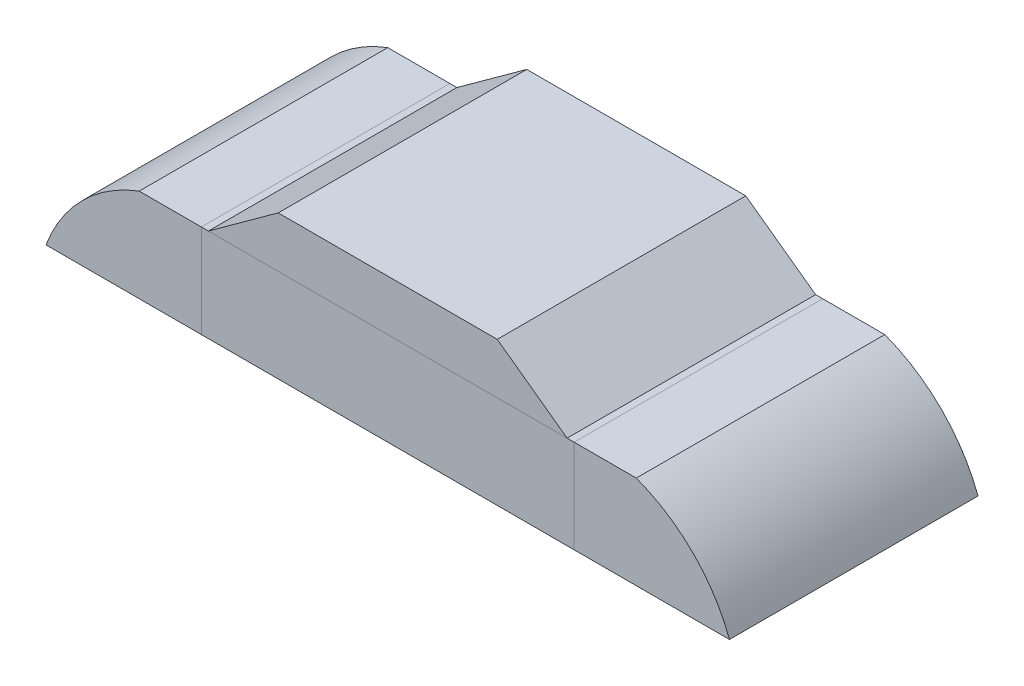
SolidWorks part; units mm, degrees
material "E-Glass Fiber"
ref_plane "Front Plane" through (0, 0, 0) normal (0, 0, 1) x (1, 0, 0)
ref_plane "Top Plane" through (0, 0, 0) normal (0, 1, 0) x (1, 0, 0)
ref_plane "Right Plane" through (0, 0, 0) normal (1, 0, 0) x (0, 0, -1)
sketch "Sketch1" plane through (0, 0, 0) normal (0, 1, 0) x (1, 0, 0)
  line L2 (-0.6, -0.4) -> (0.6, -0.4)
  line L3 (-0.6, -0.4) -> (-0.6, 0.4)
  line L4 (-0.6, 0.4) -> (0.6, 0.4)
  line L6 (0.6, -0.4) -> (0.6, 0.4)
  line L7 (-0.6, -0.4) -> (0.6, 0.4) construction
  line L8 (-0.6, 0.4) -> (0.6, -0.4) construction
  point P0 (0, 0)
  dimension "D1" = 1.2
  dimension "D2" = 0.8
extrude "Boss-Extrude1" add sketch "Sketch1" along normal blind 0.3
sketch "Sketch3" plane through (0, 0, 0) normal (0, 0, 1) x (1, 0, 0)
  line L0 (0, 0.8092) -> (0, -0.2421) construction
  line L2 (0, 0.4) -> (0.2, 0.4)
  line L3 (0, 0.4) -> (0, 0.3)
  line L4 (0, 0.3) -> (0.2, 0.3)
  line L5 (0.2, 0.4) -> (0.2, 0.3)
  line L8 (-0.6, 0.3) -> (0.6, 0.3) construction
  dimension "D1" = 0.4
  dimension "D2" = 0.1
revolve "Revolve1" add sketch "Sketch3" angle 360 about L0
sketch "Esquisse1" plane through (0, 0, 0) normal (0, 0, 1) x (1, 0, 0)
  line L0 (-0.6, 0.3) -> (-0.8, 0.3)
  line L1 (-1.1, 0) -> (-0.6, 0)
  line L2 (-0.6, 0) -> (-0.6, 0.3)
  arc A0 (-0.8, 0.3) -> (-1.1, 0) centre (-0.6213, -0.1787) ccw
  dimension "D1" = 0.2
  dimension "D2" = 0.5
extrude "Boss.-Extru.1" add sketch "Esquisse1" along normal mid plane 0.8 separate body
mirror "Symétrie2" about plane through (0, 0, 0) normal (1, 0, 0) of bodies 110
sketch "Sketch2" plane through (0, 0, 0) normal (0, 0, 1) x (1, 0, 0)
  line L0 (0.5773, 0.3) -> (-0.5773, 0.3)
  line L2 (0.6, 0.3) -> (-0.6, 0.3) construction
  line L3 (0.3524, 0.463) -> (-0.3524, 0.463)
  line L4 (0, 0.463) -> (0, 0.3) construction
  line L8 (0, 0.3) -> (0, 0) construction
  line L9 (0.6, 0) -> (-0.6, 0) construction
  line L10 (0.5773, 0.3) -> (0.3524, 0.463)
  line L11 (-0.3524, 0.463) -> (-0.5773, 0.3)
extrude "Boss-Extrude5" add sketch "Sketch2" along normal mid plane 0.8 separate body
